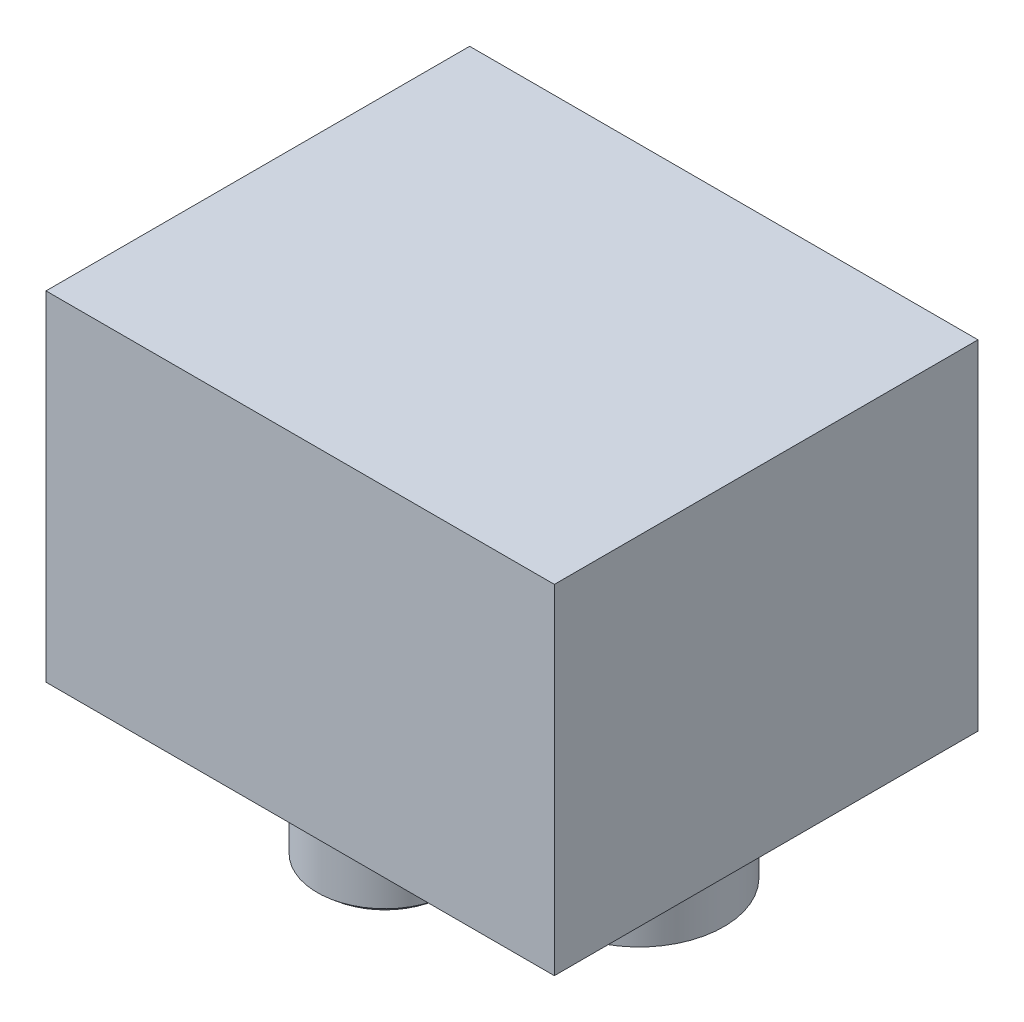
SolidWorks part; units mm, degrees
ref_plane "Front Plane" through (0, 0, 0) normal (0, 0, 1) x (1, 0, 0)
ref_plane "Top Plane" through (0, 0, 0) normal (0, 1, 0) x (1, 0, 0)
ref_plane "Right Plane" through (0, 0, 0) normal (1, 0, 0) x (0, 0, -1)
sketch "Sketch1" plane through (0, 0, 0) normal (0, 0, 1) x (1, 0, 0)
  line L1 (0, 0) -> (76.2, 0)
  line L2 (0, 0) -> (0, 50.8)
  line L3 (0, 50.8) -> (76.2, 50.8)
  line L4 (76.2, 0) -> (76.2, 50.8)
  dimension "D1" = 76.2
  dimension "D2" = 50.8
extrude "Boss-Extrude1" add sketch "Sketch1" along normal mid plane 63.5
sketch "Sketch3" plane through (0, 0, 0) normal (0, 0, 1) x (1, 0, 0)
  line L0 (12.7, 0) -> (12.7, -12.7)
  line L1 (0, 0) -> (76.2, 0) construction
  line L2 (12.7, -12.7) -> (8.89, -12.7)
  line L3 (8.89, -12.7) -> (8.89, -28.575)
  line L4 (8.89, -28.575) -> (19.05, -28.575) construction
  line L5 (19.05, -28.575) -> (19.05, 0)
  line L6 (12.7, 0) -> (19.05, 0)
  line L7 (19.05, -31.75) -> (19.05, -28.575)
  line L8 (0, 50.8) -> (0, 0) construction
  arc A0 (8.89, -28.575) -> (19.05, -31.75) centre (17.1831, -19.8804) ccw
  dimension "D6" = 12.0155
  dimension "D1" = 12.7
  dimension "D2" = 19.05
  dimension "D3" = 6.35
  dimension "D4" = 10.16
  dimension "D5" = 19.05
  dimension "D7" = 3.175
revolve "Revolve1" add sketch "Sketch3" angle 360 about L5
sketch "Sketch4" plane through (0, 0, 0) normal (0, 0, 1) x (1, 0, 0)
  line L0 (0, 0) -> (76.2, 0) construction
  line L1 (44.45, 0) -> (57.15, 0)
  line L2 (44.45, 0) -> (44.45, -12.7)
  line L3 (44.45, -12.7) -> (57.15, -12.7)
  line L4 (57.15, 0) -> (57.15, -12.7)
  line L5 (76.2, 0) -> (76.2, 50.8) construction
  dimension "D1" = 12.7
  dimension "D2" = 19.05
  dimension "D3" = 12.7
revolve "Revolve2" add sketch "Sketch4" angle 360 about L4
